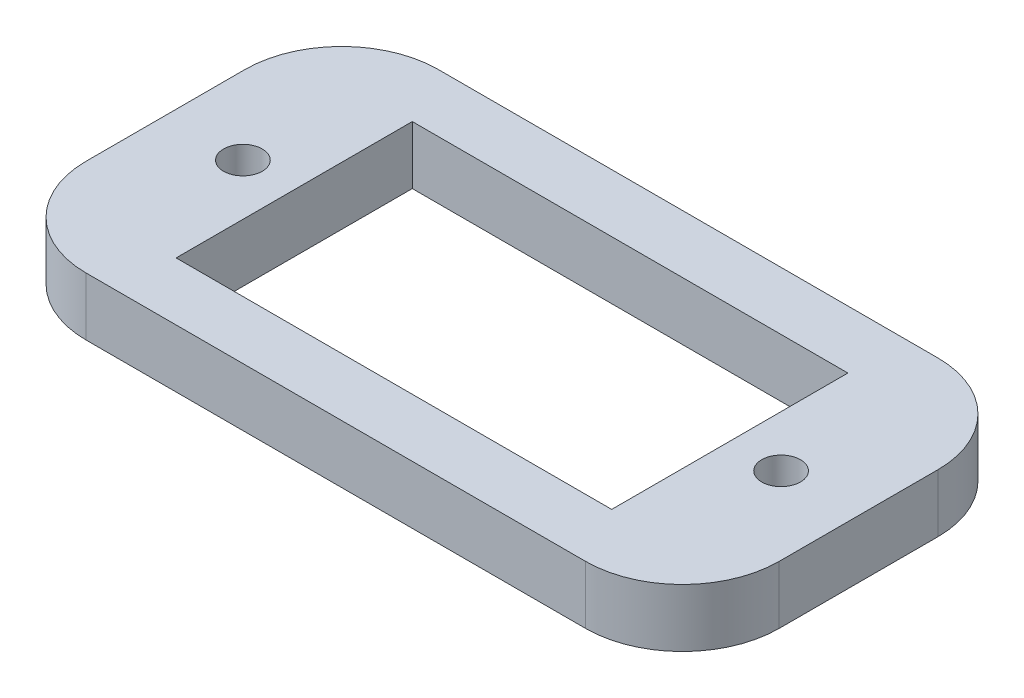
SolidWorks part; units mm, degrees
material "Acrylic (Medium-high impact)"
ref_plane "Plano frontal" through (0, 0, 0) normal (0, 0, 1) x (1, 0, 0)
ref_plane "Plano superior" through (0, 0, 0) normal (0, 1, 0) x (1, 0, 0)
ref_plane "Plano direito" through (0, 0, 0) normal (1, 0, 0) x (0, 0, -1)
sketch "Sketch1" plane through (0, 0, 0) normal (0, 1, 0) x (1, 0, 0)
  line L0 (-17.9, 9.1) -> (17.9, 9.1)
  line L1 (-11.25, 6.1) -> (11.25, 6.1)
  line L2 (-11.25, 6.1) -> (-11.25, -6.1)
  line L3 (-11.25, -6.1) -> (11.25, -6.1)
  line L4 (11.25, 6.1) -> (11.25, -6.1)
  line L5 (-55, 0) -> (55, 0) construction
  line L6 (-17.9, -9.1) -> (17.9, -9.1)
  line L7 (0, -55) -> (0, 55) construction
  line L8 (-17.9, 9.1) -> (-17.9, -9.1)
  line L9 (17.9, 9.1) -> (17.9, -9.1)
  circle A0 centre (-13.9, 0) radius 1
  circle A1 centre (13.9, 0) radius 1
  point P4 (0, 6.1)
  point P6 (-11.25, 0)
  point P9 (0, 9.1)
  dimension "D4" = 2
  dimension "D5" = 27.8
  dimension "D6" = 3
  dimension "D1" = 22.5
  dimension "D2" = 12.2
  dimension "D3" = 3
extrude "Boss-Extrude1" add sketch "Sketch1" along normal mid plane 3
fillet "Fillet1" radius 5 4 edges at (-17.9, 0, 9.1) (17.9, 0, 9.1) (17.9, 0, -9.1) (-17.9, 0, -9.1)
